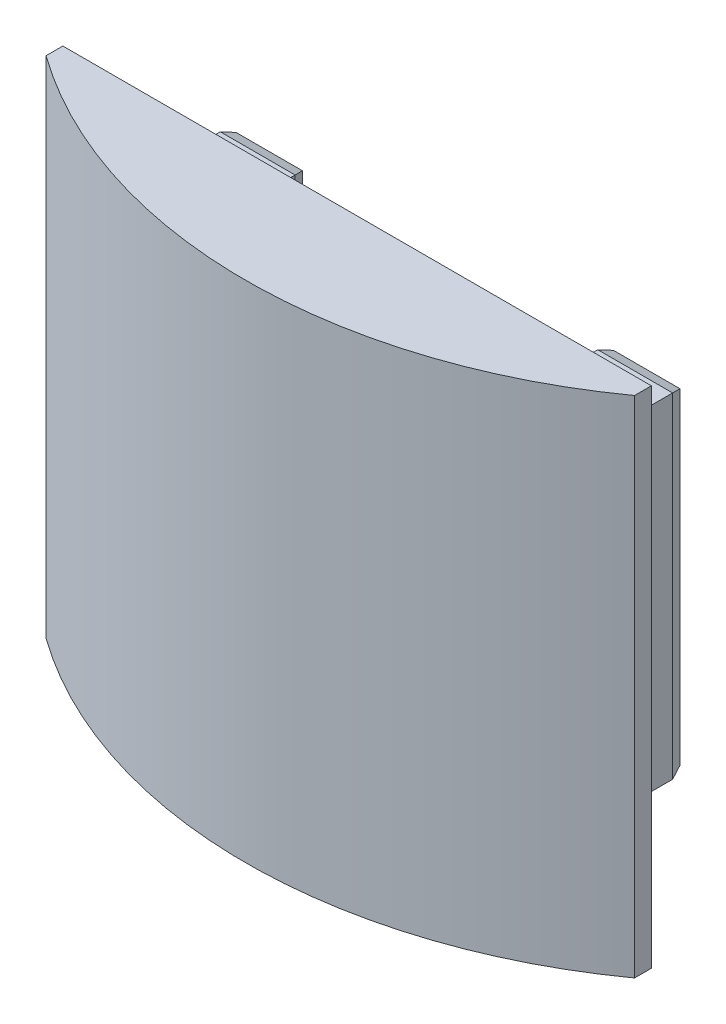
SolidWorks part; units mm, degrees
ref_plane "Спереди" through (0, 0, 0) normal (0, 0, 1) x (1, 0, 0)
ref_plane "Сверху" through (0, 0, 0) normal (0, 1, 0) x (1, 0, 0)
ref_plane "Справа" through (0, 0, 0) normal (1, 0, 0) x (0, 0, -1)
sketch "Sketch2" plane through (0, 0, 0) normal (0, 0, 1) x (1, 0, 0)
  line L1 (26.9, -19.9) -> (-26.9, -19.9)
  line L2 (26.9, -19.9) -> (26.9, 19.9)
  line L3 (26.9, 19.9) -> (-26.9, 19.9)
  line L4 (-26.9, -19.9) -> (-26.9, 19.9)
  line L5 (26.9, -19.9) -> (-26.9, 19.9) construction
  line L6 (26.9, 19.9) -> (-26.9, -19.9) construction
  point P0 (0, 0)
  dimension "D1" = 53.8
  dimension "D2" = 39.8
extrude "Boss-Extrude1" add sketch "Sketch2" along normal blind 12
sketch "Sketch3" plane through (0, 0, 12) normal (0, 0, 1) x (1, 0, 0)
  line L0 (0, 19.9) -> (0, -19.9) construction
  line L1 (35, -30) -> (-35, -30)
  line L2 (35, -30) -> (35, 30)
  line L3 (35, 30) -> (-35, 30)
  line L4 (-35, -30) -> (-35, 30)
  line L5 (35, -30) -> (-35, 30) construction
  line L6 (35, 30) -> (-35, -30) construction
  line L7 (26.9, 19.9) -> (-26.9, 19.9) construction
  line L8 (-26.9, -19.9) -> (26.9, -19.9) construction
  point P0 (0, 0)
  point P7 (0, 0)
  dimension "D1" = 70
  dimension "D2" = 60
  dimension "D3" = 0
extrude "Boss-Extrude2" add sketch "Sketch3" along normal blind 31.5
sketch "Sketch4" plane through (0, 19.9, 0) normal (0, 1, 0) x (1, 0, 0)
  line L0 (26.9, -4.6) -> (-26.9, -4.6) construction
  line L1 (26.9, -12) -> (26.9, 0) construction
  line L2 (-26.9, -12) -> (-26.9, 0) construction
  line L3 (26.9, -12) -> (-26.9, -12) construction
  circle A0 centre (22.5, -4.6) radius 2.1
  circle A1 centre (-22.5, -4.6) radius 2.1
  point P12 (0, -4.6)
  dimension "D2" = 4.2
  dimension "D3" = 4.2
  dimension "D1" = 7.4
  dimension "D4" = 45
  dimension "D5" = 22.5
extrude "Cut-Extrude1" cut sketch "Sketch4" against normal through all
sketch "Sketch5" plane through (0, 0, 0) normal (0, 0, -1) x (-1, 0, 0)
  line L0 (-26.9, 19.9) -> (26.9, 19.9) construction
  line L1 (18, -19.9) -> (-18, -19.9)
  line L2 (18, -19.9) -> (18, 19.9)
  line L3 (18, 19.9) -> (-18, 19.9)
  line L4 (-18, -19.9) -> (-18, 19.9)
  line L5 (18, -19.9) -> (-18, 19.9) construction
  line L6 (18, 19.9) -> (-18, -19.9) construction
  point P0 (0, 0)
  dimension "D1" = 36
extrude "Cut-Extrude2" cut sketch "Sketch5" against normal up to surface (12 mm away) up to face at (0, 0, 12)
chamfer "Chamfer1" distance 0.5 angle 70 8 edges at (26.9, 0, 0) (22.45, 19.9, 0) (18, 0, 0) (22.45, -19.9, 0) (-26.9, 0, 0) (-22.45, -19.9, 0) (-18, 0, 0) (-22.45, 19.9, 0)
sketch "Sketch27" plane through (0, -30, 0) normal (0, -1, 0) x (1, 0, 0)
  line L0 (-35, 43.5) -> (-35, 12) construction
  line L1 (35, 43.5) -> (35, 12) construction
  line L2 (-35, 14) -> (-35, 12) construction
  line L3 (-35, 12) -> (35, 12) construction
  line L4 (35, 12) -> (35, 14) construction
  arc A0 (-35, 14) -> (35, 14) centre (0, -34.734) cw
  arc A1 (-35, 14) -> (35, 14) centre (0, 72.1657) cw
  dimension "D2" = 60
  dimension "D1" = 2
extrude "Cut-Extrude13" cut sketch "Sketch27" against normal through all
